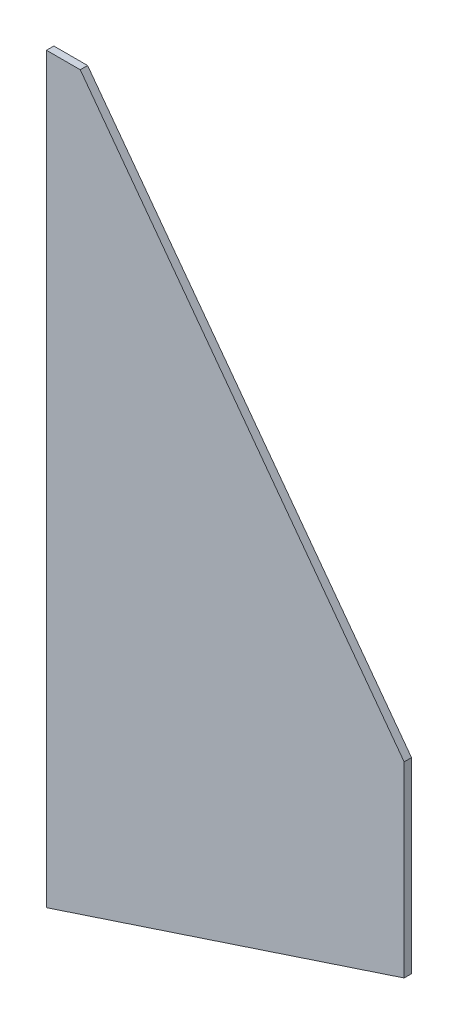
SolidWorks part; units mm, degrees
ref_plane "Front Plane" through (0, 0, 0) normal (0, 0, 1) x (1, 0, 0)
ref_plane "Top Plane" through (0, 0, 0) normal (0, 1, 0) x (1, 0, 0)
ref_plane "Right Plane" through (0, 0, 0) normal (1, 0, 0) x (0, 0, -1)
sketch "Sketch1" plane through (0, 0, 0) normal (0, 0, 1) x (1, 0, 0)
  line L0 (-65.1468, 198.8691) -> (-65.1468, -103.3909)
  line L1 (-65.1468, -103.3909) -> (80.4444, -55.388)
  line L2 (80.4444, -55.388) -> (80.4444, 20.812)
  line L4 (-65.1468, 198.8691) -> (-51.4054, 198.8691)
  line L5 (-51.4054, 198.8691) -> (80.4444, 20.812)
  dimension "D1" = 302.26
  dimension "D2" = 76.2
  dimension "D3" = 13.7414
extrude "Boss-Extrude1" add sketch "Sketch1" along normal blind 2.9972
